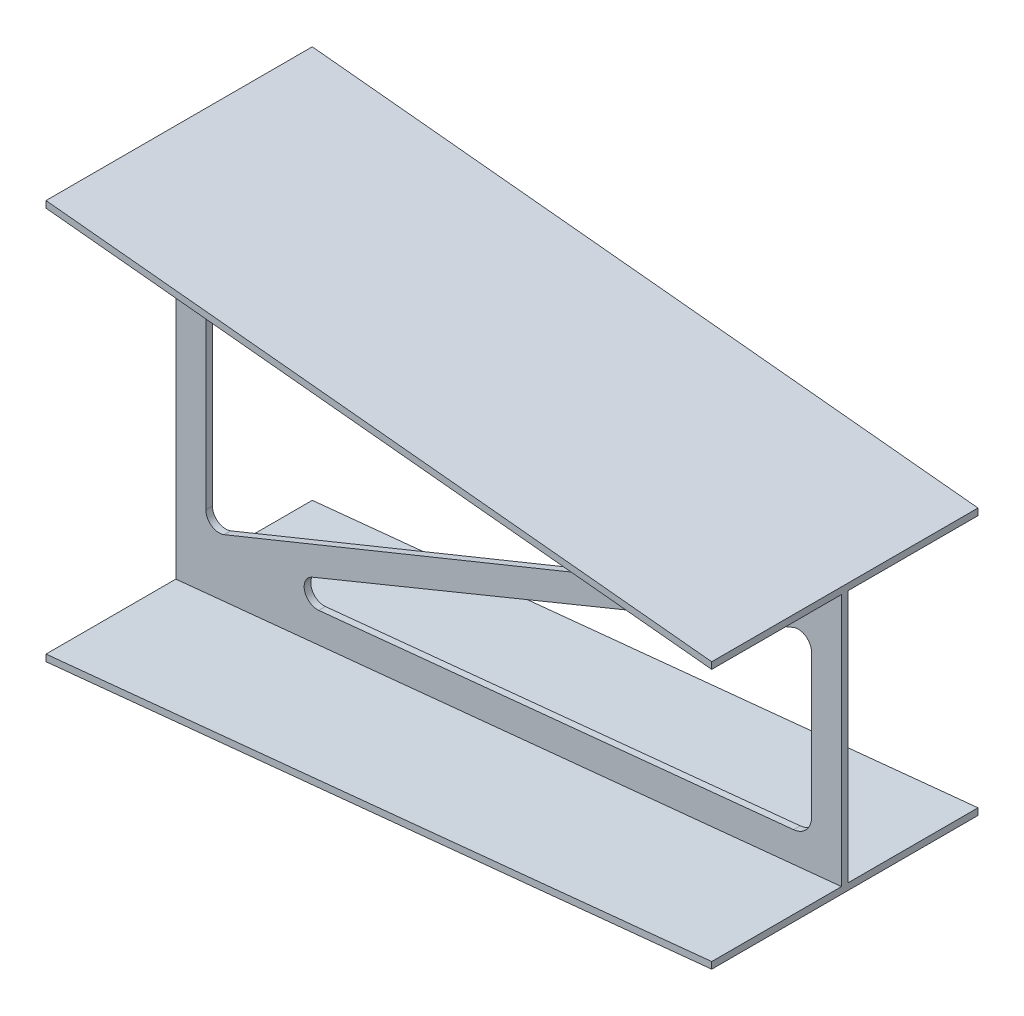
SolidWorks part; units mm, degrees
ref_plane "Front Plane" through (0, 0, 0) normal (0, 0, 1) x (1, 0, 0)
ref_plane "Top Plane" through (0, 0, 0) normal (0, 1, 0) x (1, 0, 0)
ref_plane "Right Plane" through (0, 0, 0) normal (1, 0, 0) x (0, 0, -1)
sketch "Sketch1" plane through (0, 0, 0) normal (1, 0, 0) x (0, 0, -1)
  line L1 (-205, 300) -> (195, 300)
  line L2 (-205, 300) -> (-205, 290)
  line L4 (195, 300) -> (195, 290)
  line L6 (-205, -290) -> (-205, -300)
  line L7 (-205, -300) -> (195, -300)
  line L8 (195, -290) -> (195, -300)
  line L15 (-205, -290) -> (-10, -290)
  line L16 (-5, 290) -> (-5, -690) construction
  line L18 (-205, 290) -> (-10, 290)
  line L19 (0, 0) -> (192.2403, 0) construction
  line L21 (-10, 290) -> (-10, -290)
  line L23 (0, 290) -> (0, -290)
  line L27 (0, 290) -> (195, 290)
  line L28 (0, -290) -> (195, -290)
  dimension "D1" = 400
  dimension "D2" = 10
  dimension "D3" = 600
  dimension "D4" = 10
ref_plane "Plane2" through (1000, 0, 0) normal (1, 0, 0) x (0, 0, -1)
sketch "Sketch4" plane through (1000, 0, -1000) normal (-1, 0, 0) x (0, 0, 1)
  line L1 (805, 200) -> (1205, 200)
  line L2 (805, 200) -> (805, 190)
  line L4 (1205, 200) -> (1205, 190)
  line L6 (805, -190) -> (805, -200)
  line L7 (805, -200) -> (1205, -200)
  line L8 (1205, -190) -> (1205, -200)
  line L15 (805, -190) -> (1000, -190)
  line L16 (1005, 390) -> (1005, -390) construction
  line L18 (805, 190) -> (1000, 190)
  line L19 (1010, -190) -> (1205, -190)
  line L21 (1000, 190) -> (1000, -190)
  line L23 (1010, 190) -> (1010, -190)
  line L24 (1010, 190) -> (1205, 190)
  line L26 (1010, 290) -> (1010, -290) construction
  line L27 (1000, 0) -> (820.2065, 0) construction
  dimension "D1" = 400
  dimension "D2" = 10
  dimension "D3" = 400
  dimension "D4" = 10
loft "Loft4" add profiles "Sketch1", "Sketch4"
sketch3d "3DSketch1"
  line L0 (955, -149.2756, 0) -> (45, -240.2756, 0)
  line L1 (45, -240.2756, 0) -> (45, 240.2756, 0)
  line L2 (45, 240.2756, 0) -> (955, 149.2756, 0)
  line L3 (955, 149.2756, 0) -> (955, -149.2756, 0)
  line L4 (927.9851, -151.977, 0) -> (214.7626, -223.2993, 0)
  line L5 (45, -177.4014, 0) -> (45, 207.1259, 0)
  line L6 (77.9851, 236.977, 0) -> (847.6955, 160.006, 0)
  line L7 (955, 92.3251, 0) -> (955, -122.1259, 0)
  line L8 (927.4215, 110.8336, 0) -> (205.194, -184.89, 0)
  line L9 (72.5346, -195.9278, 0) -> (853.24, 121.5788, 0)
  arc A1 (45, 207.1259, 0) -> (77.9851, 236.977, 0) centre (75, 207.1259, 0) ccw
  arc A3 (955, -122.1259, 0) -> (927.9851, -151.977, 0) centre (925, -122.1259, 0) ccw
  arc A4 (45, -177.4014, 0) -> (72.5346, -195.9278, 0) centre (65, -177.4014, 0) ccw
  arc A5 (214.7626, -223.2993, 0) -> (205.194, -184.89, 0) centre (212.7726, -203.3986, 0) ccw
  arc A6 (847.6955, 160.006, 0) -> (853.24, 121.5788, 0) centre (845.7054, 140.1053, 0) ccw
  arc A7 (927.4215, 110.8336, 0) -> (955, 92.3251, 0) centre (935, 92.3251, 0) ccw
  point P11 (75, 207.1259, -30)
  point P14 (65, -177.4014, 20)
  point P19 (925, -122.1259, -30)
  point P21 (212.7726, -203.3986, -20)
  point P24 (845.7054, 140.1053, -20)
  point P27 (935, 92.3251, -20)
  dimension "D2" = 20
  dimension "D1" = 45
extrude "Cut-Extrude2" cut sketch "3DSketch1" along direction (0, 0, 1) on the side of the normal through all
